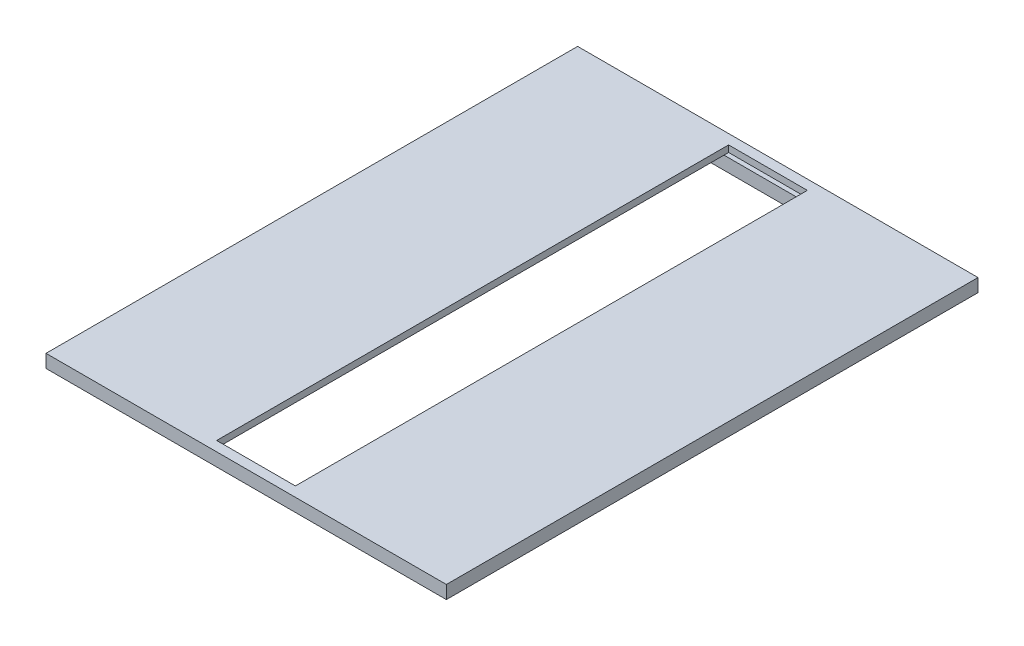
SolidWorks part; units mm, degrees
ref_plane "Front Plane" through (0, 0, 0) normal (0, 0, 1) x (1, 0, 0)
ref_plane "Top Plane" through (0, 0, 0) normal (0, 1, 0) x (1, 0, 0)
ref_plane "Right Plane" through (0, 0, 0) normal (1, 0, 0) x (0, 0, -1)
sketch "Sketch1" plane through (0, 0, 0) normal (0, 1, 0) x (1, 0, 0)
  line L1 (76.25, -101.25) -> (-76.25, -101.25)
  line L2 (76.25, -101.25) -> (76.25, 101.25)
  line L3 (76.25, 101.25) -> (-76.25, 101.25)
  line L4 (-76.25, -101.25) -> (-76.25, 101.25)
  line L5 (76.25, -101.25) -> (-76.25, 101.25) construction
  line L6 (76.25, 101.25) -> (-76.25, -101.25) construction
  point P0 (0, 0)
  dimension "D1" = 202.5
  dimension "D2" = 152.5
extrude "Boss-Extrude1" add sketch "Sketch1" against normal blind 5
sketch "Sketch3" plane through (0, -5, 0) normal (0, -1, 0) x (1, 0, 0)
  line L1 (75.75, -100.75) -> (-75.75, -100.75)
  line L2 (75.75, -100.75) -> (75.75, 100.75)
  line L3 (75.75, 100.75) -> (-75.75, 100.75)
  line L4 (-75.75, -100.75) -> (-75.75, 100.75)
  line L5 (75.75, -100.75) -> (-75.75, 100.75) construction
  line L6 (75.75, 100.75) -> (-75.75, -100.75) construction
  point P0 (0, 0)
  dimension "D1" = 201.5
  dimension "D2" = 151.5
extrude "Cut-Extrude1" cut sketch "Sketch3" against normal blind 2.5
sketch "Sketch5" plane through (0, -2.5, 0) normal (0, -1, 0) x (1, 0, 0)
  line L0 (0, -100.75) -> (0, 100.75) construction
  line L1 (-75.75, -100.75) -> (75.75, -100.75) construction
  line L2 (75.75, 100.75) -> (-75.75, 100.75) construction
  line L3 (73.25, 98.25) -> (-73.25, 98.25)
  line L4 (-73.25, 98.25) -> (-73.25, -98.25)
  line L5 (-73.25, -98.25) -> (73.25, -98.25)
  line L7 (70.75, -95.75) -> (-70.75, -95.75)
  line L8 (-70.75, -95.75) -> (-70.75, 95.75)
  line L9 (-70.75, 95.75) -> (70.75, 95.75)
  line L11 (-75.75, 100.75) -> (-75.75, -100.75) construction
  line L12 (-75.75, -100.75) -> (75.75, -100.75) construction
  line L13 (70.75, -95.75) -> (70.75, 95.75)
  line L14 (73.25, 98.25) -> (73.25, -98.25)
  point P14 (0, 98.25)
  point P19 (0, -95.75)
  point P20 (0, -98.25)
  point P22 (0, 95.75)
  dimension "D1" = 2.5
  dimension "D2" = 2.5
  dimension "D3" = 2.5
  dimension "D4" = 2.5
  dimension "D5" = 2.5
  dimension "D6" = 2.5
extrude "Boss-Extrude3" add sketch "Sketch5" along normal blind 5
sketch "Sketch6" plane through (0, 0, 0) normal (0, 1, 0) x (1, 0, 0)
  line L1 (15, -97.5) -> (-15, -97.5)
  line L2 (15, -97.5) -> (15, 97.5)
  line L3 (15, 97.5) -> (-15, 97.5)
  line L4 (-15, -97.5) -> (-15, 97.5)
  line L5 (15, -97.5) -> (-15, 97.5) construction
  line L6 (15, 97.5) -> (-15, -97.5) construction
  point P0 (0, 0)
  dimension "D1" = 30
  dimension "D2" = 195
extrude "Cut-Extrude4" cut sketch "Sketch6" against normal blind 2.5
sketch "Sketch7" plane through (0, -2.5, 0) normal (0, -1, 0) x (1, 0, 0)
  line L0 (0, 95.75) -> (0, -95.75) construction
  line L1 (70.75, 95.75) -> (-70.75, 95.75) construction
  line L2 (-70.75, -95.75) -> (70.75, -95.75) construction
  line L3 (-25, 92.75) -> (-25, -92.75)
  line L6 (-20, -92.75) -> (-20, 92.75)
  line L12 (-25, -92.75) -> (-20, -92.75)
  line L13 (-25, 92.75) -> (-20, 92.75)
  line L14 (-70.75, -95.75) -> (-15, -95.75) construction
  line L15 (25, -92.75) -> (20, -92.75)
  line L16 (25, 92.75) -> (20, 92.75)
  line L17 (25, 92.75) -> (25, -92.75)
  line L18 (20, -92.75) -> (20, 92.75)
  dimension "D1" = 20
  dimension "D2" = 5
  dimension "D3" = 3
  dimension "D4" = 3
extrude "Boss-Extrude5" add sketch "Sketch7" along normal blind 3
